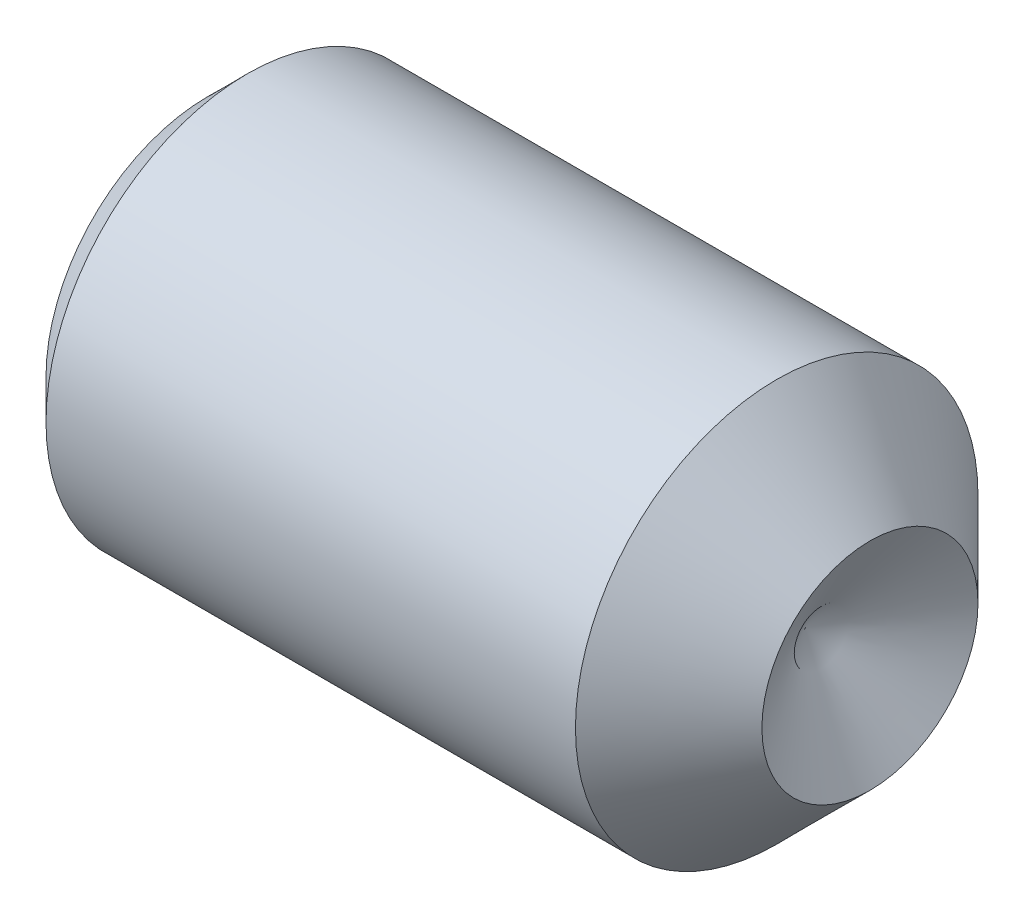
SolidWorks part; units mm, degrees
material "Alloy Steel"
ref_plane "Plane1" through (0, 0, 0) normal (0, 0, 1) x (1, 0, 0)
ref_plane "Plane2" through (0, 0, 0) normal (0, 1, 0) x (1, 0, 0)
ref_plane "Plane3" through (0, 0, 0) normal (1, 0, 0) x (0, 0, -1)
sketch "BodySke" plane through (0, 0, 0) normal (0, 0, 1) x (1, 0, 0)
  line L0 (0, 0) -> (0, 1.9406)
  line L1 (0, 1.9406) -> (0.4724, 2.413)
  line L2 (0.4724, 2.413) -> (6.8199, 2.413)
  line L3 (6.8199, 2.413) -> (7.9375, 1.2954)
  line L4 (7.1591, 0) -> (0, 0)
  line L5 (-12.7, 0) -> (88.9, 0) construction
  line L6 (7.1591, 0) -> (7.9375, 1.2954)
  line L7 (7.9375, 1.2954) -> (7.9375, 10.8204) construction
  line L8 (0, -1.9406) -> (0.4724, -2.413) construction
  line L9 (7.1591, 0) -> (7.9375, -1.2954) construction
  line L10 (6.8199, -2.413) -> (7.9375, -1.2954) construction
  line L11 (0.7925, 15.875) -> (0.7925, -3.175) construction
  dimension "Length" = 7.9375
  dimension "Diameter" = 4.826
  dimension "Drive_ch_ang" = 45
  dimension "Minor_dia" = 3.8811
  dimension "Cup_nose_ang" = 45
  dimension "Cup_ang" = 118
  dimension "Cup_dia" = 2.5908
  dimension "Advance" = 0.7925
revolve "BaseBody" add sketch "BodySke" angle 360 about L5
cosmetic thread "ThreadCosmetic" parameters "Thread_minor"=3.8811
sketch "Sketch2" plane through (0, 0, 0) normal (-1, 0, 0) x (0, 0, 1)
  line L0 (0.687, 1.19) -> (-0.687, 1.19)
  line L1 (-0.687, 1.19) -> (-1.3741, 0)
  line L2 (0.687, 1.19) -> (1.3741, 0)
  line L3 (0.687, -1.19) -> (1.3741, 0)
  line L4 (0.687, -1.19) -> (-0.687, -1.19)
  line L5 (-0.687, -1.19) -> (-1.3741, 0)
  dimension "Hex_size" = 2.38
  dimension "D2" = 1.19
  dimension "D3" = 1.19
extrude "Hex" cut sketch "Sketch2" against normal blind 2.54
sketch "Sketch4" plane through (0, 4.7709, -0.5249) normal (-1, 0, 0) x (0, 0, 1)
  line L0 (0.5249, -4.7709) -> (1.9854, -4.7709)
  line L1 (0.5249, -4.7709) -> (6.6732, -1.2211) construction
  line L2 (0.5249, -4.7709) -> (1.2551, -3.506)
  line L3 (1.7258, -4.4441) -> (1.9182, -4.333)
  line L4 (1.4083, -3.8942) -> (1.6007, -3.7831)
  arc A0 (1.7258, -4.4441) -> (1.4083, -3.8942) centre (0.5249, -4.7709) ccw
  arc A1 (1.9854, -4.7709) -> (1.9182, -4.333) centre (0.5249, -4.7709) ccw
  arc A2 (1.2551, -3.506) -> (1.6007, -3.7831) centre (0.5249, -4.7709) cw
  circle A3 centre (0.5249, -4.7709) radius 1.2446 construction
  circle A4 centre (0.5249, -4.7709) radius 1.4605 construction
  dimension "D1" = 30
  dimension "Spline_n_dim" = 2.4892
  dimension "Spline_m_dim" = 2.921
  dimension "Spline_a_dim" = 60
  dimension "D3" = 0.3175
  dimension "Spline_p_dim" = 0.635
extrude "Spline" [suppressed] cut sketch "Sketch4" against normal blind 2.032
pattern_circular "CirPattern1" [suppressed] count 6 every 60 about axis through (-12.7, 0, 0) along (1, 0, 0)
sketch "ThdSchSke" plane through (0, 0, 0) normal (0, 0, 1) x (1, 0, 0)
  line L0 (0.4724, -1.9406) -> (0.1416, -2.413)
  line L1 (0.4724, -1.9406) -> (0.8032, -2.413)
  line L2 (0.8032, -2.413) -> (0.8032, -3.0162)
  line L3 (-3.175, 0) -> (5.1513, 0) construction
  line L4 (0.4724, 2.413) -> (0.4724, -2.413) construction
  line L5 (0.8032, -3.0162) -> (0.1416, -3.0162)
  line L6 (0.1416, -3.0162) -> (0.1416, -2.413)
  dimension "Thread_minor" = 3.8811
  dimension "Diameter" = 4.826
  dimension "SideAngle" = 55
  dimension "VeeAngle" = 70
  dimension "Overcut" = 6.0325
revolve "ThreadSchematic" [suppressed] cut sketch "ThdSchSke" angle 360 about L3
pattern_linear "ThdSchPat" [suppressed]
sketch3d "3DSketch1"
  circle A0 centre (7.9375, 0, 0) radius 1.2954 construction
  point P0 (7.9375, 0, 0)
  point P4 (6.6421, 0, 0)
equation "\"D2@Sketch2\" = \"Hex_size@Sketch2\" / 2"
equation "\"D3@Sketch2\" = \"Hex_size@Sketch2\" / 2"
equation "\"Thread_minor@ThreadCosmetic\" = \"Minor_dia@BodySke\""
equation "\"D1@Sketch4\" = \"Spline_a_dim@Sketch4\" / 2"
equation "\"D3@Sketch4\" = \"Spline_p_dim@Sketch4\" / 2"
equation "\"D2@CirPattern1\" = \"Spline_a_dim@Sketch4\""
equation "\"Num_teeth@CirPattern1\" = 360 / \"D2@CirPattern1\""
equation "\"Thread_minor@ThdSchSke\" = \"Thread_minor@ThreadCosmetic\""
equation "\"Diameter@ThdSchSke\" = \"Diameter@BodySke\""
equation "\"Overcut@ThdSchSke\" = \"Diameter@BodySke\" * 1.25"
equation "\"Num_threads@ThdSchPat\" = int( (\"Length@BodySke\" - ( ( ( \"Diameter@BodySke\" - \"Minor_dia@BodySke\" ) * 0.5 ) / tan( \"Drive_ch_ang@BodySke\" * 0.017453292 ) ) - ( ( ( \"Diameter@BodySke\" - \"Cup_dia@BodySke\" ) * 0.5 ) * tan( \"Cup_nose_ang@BodySke\" * 0.017453292 ) ) ) / \"Advance@BodySke\" + 0.999 )  + 1"
equation "\"Advance@ThdSchPat\" = (\"Length@BodySke\" - ( ( ( \"Diameter@BodySke\" - \"Minor_dia@BodySke\" ) * 0.5 ) / tan( \"Drive_ch_ang@BodySke\" * 0.017453292 ) ) - ( ( ( \"Diameter@BodySke\" - \"Cup_dia@BodySke\" ) * 0.5 ) * tan( \"Cup_nose_ang@BodySke\" * 0.017453292 ) ) ) /  (\"Num_threads@ThdSchPat\" - 1) 'relax it"
equation "' \"Num_threads@ThdSchPat\" = \"Num_threads@ThdSchPat\" - sgn( \"Num_threads@ThdSchPat\" - 1) '---chamfered tips only---"
